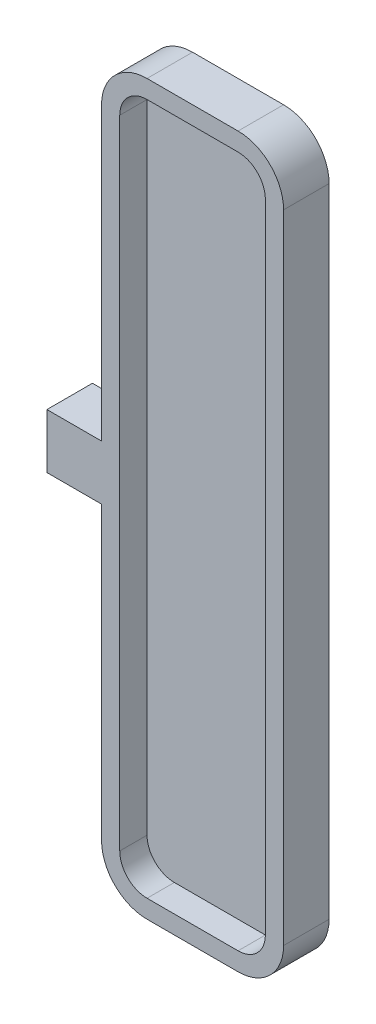
SolidWorks part; units mm, degrees
ref_plane "Front Plane" through (0, 0, 0) normal (0, 0, 1) x (1, 0, 0)
ref_plane "Top Plane" through (0, 0, 0) normal (0, 1, 0) x (1, 0, 0)
ref_plane "Right Plane" through (0, 0, 0) normal (1, 0, 0) x (0, 0, -1)
sketch "Sketch1" plane through (0, 0, 0) normal (0, 0, 1) x (1, 0, 0)
  line L1 (-10, -40) -> (10, -40)
  line L2 (-10, -40) -> (-10, 40)
  line L3 (-10, 40) -> (10, 40)
  line L4 (10, -40) -> (10, 40)
  line L5 (-10, -40) -> (10, 40) construction
  line L6 (-10, 40) -> (10, -40) construction
  point P0 (0, 0)
  dimension "D1" = 20
  dimension "D2" = 80
extrude "Boss-Extrude1" add sketch "Sketch1" along normal blind 5
fillet "Fillet1" radius 5 4 edges at (10, -40, 2.5) (-10, -40, 2.5) (-10, 40, 2.5) (10, 40, 2.5)
shell "Shell2" thickness 2
sketch "Sketch2" plane through (0, 0, 0) normal (0, 0, 1) x (1, 0, 0)
  line L0 (-10, 0) -> (-18.0132, 0) construction
  line L1 (-10, 35) -> (-10, -35) construction
  line L3 (-10, 3) -> (-16, 3)
  line L4 (-10, 3) -> (-10, -3)
  line L5 (-10, -3) -> (-16, -3)
  line L6 (-16, 3) -> (-16, -3)
  dimension "D1" = 6
  dimension "D2" = 6
extrude "Boss-Extrude2" add sketch "Sketch2" along normal blind 5
sketch "Sketch3" plane through (-16, 0, 0) normal (-1, 0, 0) x (0, 0, 1)
  line L0 (2.5, 3) -> (2.5, -3) construction
  line L1 (5, 3) -> (0, 3) construction
  line L2 (5, -3) -> (0, -3) construction
  circle A0 centre (2.5, 0) radius 1.425
  dimension "D1" = 2.85
extrude "Cut-Extrude1" cut sketch "Sketch3" against normal blind 4
